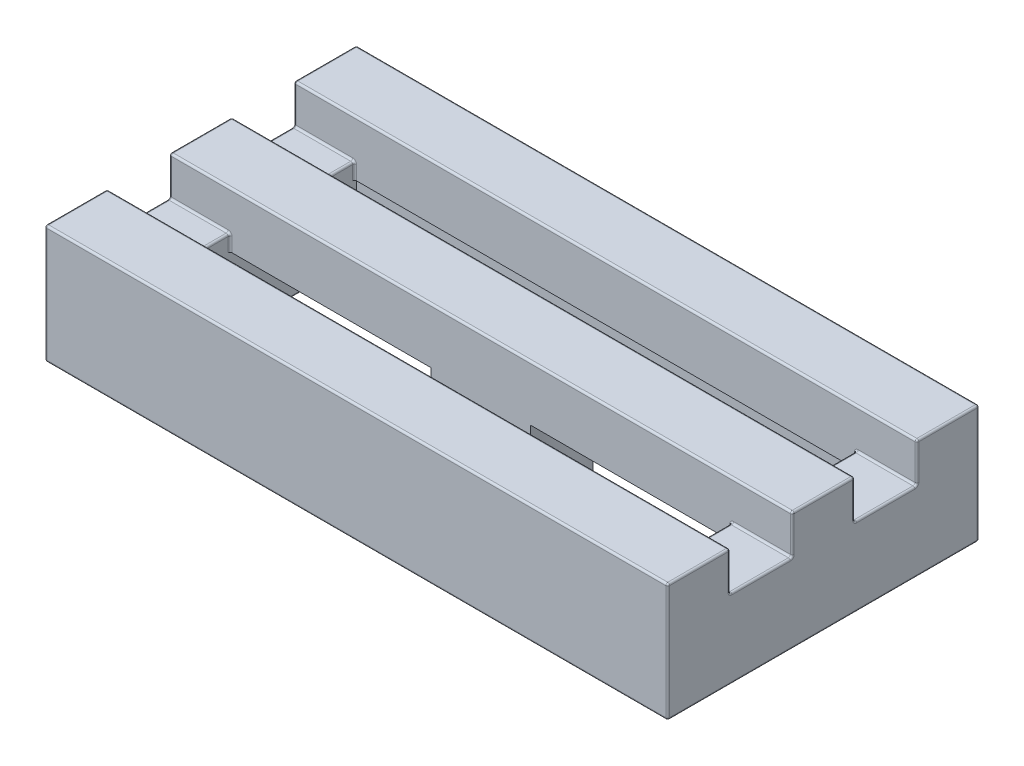
SolidWorks part; units mm, degrees
material "Grey"
ref_plane "Front Plane" through (0, 0, 0) normal (0, 0, 1) x (1, 0, 0)
ref_plane "Top Plane" through (0, 0, 0) normal (0, 1, 0) x (1, 0, 0)
ref_plane "Right Plane" through (0, 0, 0) normal (1, 0, 0) x (0, 0, -1)
sketch "Sketch1" plane through (0, 0, 0) normal (0, 1, 0) x (1, 0, 0)
  line L1 (-3.98, 3.98) -> (3.98, 3.98)
  line L2 (-3.98, 3.98) -> (-3.98, -3.98)
  line L3 (-3.98, -3.98) -> (3.98, -3.98)
  line L4 (3.98, 3.98) -> (3.98, -3.98)
  line L5 (-3.98, 3.98) -> (3.98, -3.98) construction
  line L6 (-3.98, -3.98) -> (3.98, 3.98) construction
  point P0 (0, 0)
  dimension "D1" = 7.96
extrude "Extrude1" add sketch "Sketch1" along normal blind 3.22
pattern_linear "LPattern1" count 2 spacing 7.96 along (1, 0, 0) of "Extrude1"
shell "Shell1" thickness 1.55
sketch "Sketch4" plane through (0, 1.67, 0) normal (0, -1, 0) x (1, 0, 0)
  line L0 (10.39, 2.43) -> (10.39, -2.43) construction
  line L1 (-2.43, 2.43) -> (10.39, 2.43) construction
  line L2 (-2.43, -2.43) -> (-2.43, 2.43) construction
  line L3 (10.39, -2.43) -> (-2.43, -2.43) construction
  line L4 (10.39, 2.43) -> (10.39, -2.43)
  line L5 (-2.43, 2.43) -> (10.39, 2.43)
  line L6 (-2.43, -2.43) -> (-2.43, 2.43)
  line L7 (10.39, -2.43) -> (-2.43, -2.43)
extrude "Extrude3" cut sketch "Sketch4" against normal blind 0.14
sketch "Sketch5" plane through (0, 1.81, 0) normal (0, -1, 0) x (1, 0, 0)
  line L0 (10.39, 2.43) -> (-2.43, 2.43) construction
  circle A0 centre (3.98, 0) radius 1.5
  circle A1 centre (3.98, 0) radius 0.64 construction
  point P5 (3.98, 2.43)
  dimension "D1" = 3
  dimension "D2" = 0.86
sketch "Sketch7" plane through (0, 0, 0) normal (0, -1, 0) x (1, 0, 0)
  line L0 (11.94, 3.98) -> (11.94, -3.98) construction
  line L1 (-3.98, 3.98) -> (11.94, 3.98) construction
  line L2 (-3.98, -3.98) -> (-3.98, 3.98) construction
  line L3 (11.94, -3.98) -> (-3.98, -3.98) construction
  line L4 (11.94, 3.98) -> (11.94, -3.98)
  line L5 (-3.98, 3.98) -> (11.94, 3.98)
  line L6 (-3.98, -3.98) -> (-3.98, 3.98)
  line L7 (11.94, -3.98) -> (-3.98, -3.98)
  line L8 (11.74, 3.78) -> (11.74, -3.78)
  line L9 (11.74, -3.78) -> (-3.78, -3.78)
  line L10 (-3.78, -3.78) -> (-3.78, 3.78)
  line L11 (-3.78, 3.78) -> (11.74, 3.78)
  dimension "D1" = 0.2
extrude "Extrude6" cut sketch "Sketch7" against normal blind 0.2
extrude "Extrude7" add sketch "Sketch5" along normal up to surface (1.81 mm away) up to face at (3.98, 0, 0)
sketch "Sketch8" plane through (11.94, 0, 0) normal (1, 0, 0) x (0, 0, -1)
  line L0 (-3.98, 3.22) -> (3.98, 3.22) construction
  line L1 (-3.98, 3.22) -> (-3.98, 0.2) construction
  line L2 (2.388, 3.22) -> (0.796, 3.22)
  line L3 (2.388, 3.22) -> (2.388, 2.22)
  line L4 (2.388, 2.22) -> (0.796, 2.22)
  line L5 (0.796, 3.22) -> (0.796, 2.22)
  line L6 (-0.796, 3.22) -> (-2.388, 3.22)
  line L7 (-0.796, 3.22) -> (-0.796, 2.22)
  line L8 (-0.796, 2.22) -> (-2.388, 2.22)
  line L9 (-2.388, 3.22) -> (-2.388, 2.22)
  dimension "D1" = 1.592
  dimension "D2" = 1.592
  dimension "D3" = 1.592
  dimension "D4" = 1
extrude "Extrude8" cut sketch "Sketch8" against normal through all
sketch "Sketch10" plane through (0, 2.22, 0) normal (0, 1, 0) x (1, 0, 0)
  line L1 (-3.98, 2.388) -> (11.94, 2.388) construction
  line L2 (-2.43, 2.388) -> (10.39, 2.388)
  line L3 (-2.43, 2.388) -> (-2.43, 0.796)
  line L4 (-2.43, 0.796) -> (10.39, 0.796)
  line L7 (10.39, 2.388) -> (10.39, 0.796)
  line L8 (-2.43, -2.43) -> (-2.43, 2.43) construction
  line L9 (-3.98, -2.388) -> (11.94, -2.388) construction
  line L10 (-2.43, -2.388) -> (10.39, -2.388)
  line L15 (-2.43, -2.388) -> (-2.43, -0.796)
  line L16 (-2.43, -0.796) -> (10.39, -0.796)
  line L17 (10.39, -2.388) -> (10.39, -0.796)
  line L18 (-3.98, -0.796) -> (11.94, -0.796) construction
  line L19 (-3.98, 0.796) -> (11.94, 0.796) construction
  line L20 (10.39, 2.43) -> (10.39, -2.43) construction
extrude "Extrude9" cut sketch "Sketch10" against normal through all
fillet "Fillet3" radius 0.05 68 edges at (-3.98, 3.22, -3.184) (11.165, 2.22, -0.796) (11.165, 2.22, -2.388) (-2.43, 2.015, -0.796) (-2.43, 2.015, -2.388) (10.39, 2.015, -2.388) (10.39, 2.015, -0.796) (-2.43, 2.22, -1.592) (10.39, 2.22, -1.592) (3.98, 3.22, 3.98) (11.165, 2.22, 2.388) (11.165, 2.22, 0.796) (11.94, 1.71, 3.98) (11.94, 1.71, -3.98) (-2.43, 2.015, 2.388) (-2.43, 2.015, 0.796) (10.39, 2.015, 0.796) (10.39, 2.015, 2.388) (-2.43, 2.22, 1.592) (10.39, 2.22, 1.592) (11.94, 3.22, 3.184) (3.98, 0, -2.43) (-2.43, 0, 0) (3.98, 0, 2.43) (10.39, 0, 0) (3.98, 0.2, 3.98) (11.94, 0.2, 0) (3.98, 0.2, -3.98) (-3.98, 0.2, 0) (3.98, 0.2, 3.78) (-3.78, 0.2, 0) (3.98, 0.2, -3.78) (11.74, 0.2, 0) (3.98, 0, 3.78) (11.74, 0.1, 3.78) (11.74, 0, 0) (11.74, 0.1, -3.78) (3.98, 0, -3.78) (-3.78, 0.1, -3.78) (-3.78, 0, 0) (-3.78, 0.1, 3.78) (3.98, 3.22, -3.98) (-3.98, 1.71, 3.98) (-3.98, 1.71, -3.98) (-3.98, 3.22, 0) (11.94, 3.22, -3.184) (-3.98, 2.72, -2.388) (3.98, 3.22, -2.388) (-3.98, 2.22, -1.592) (-3.205, 2.22, -2.388) (-3.98, 2.72, -0.796) (-3.205, 2.22, -0.796) (3.98, 3.22, -0.796) (11.94, 2.72, -2.388) (11.94, 2.72, -0.796) (11.94, 2.22, -1.592) (-3.98, 3.22, 3.184) (11.94, 3.22, 0) (-3.98, 2.72, 0.796) (3.98, 3.22, 0.796) (-3.98, 2.22, 1.592) (-3.205, 2.22, 0.796) (-3.98, 2.72, 2.388) (-3.205, 2.22, 2.388) (3.98, 3.22, 2.388) (11.94, 2.72, 0.796) (11.94, 2.72, 2.388) (11.94, 2.22, 1.592)
